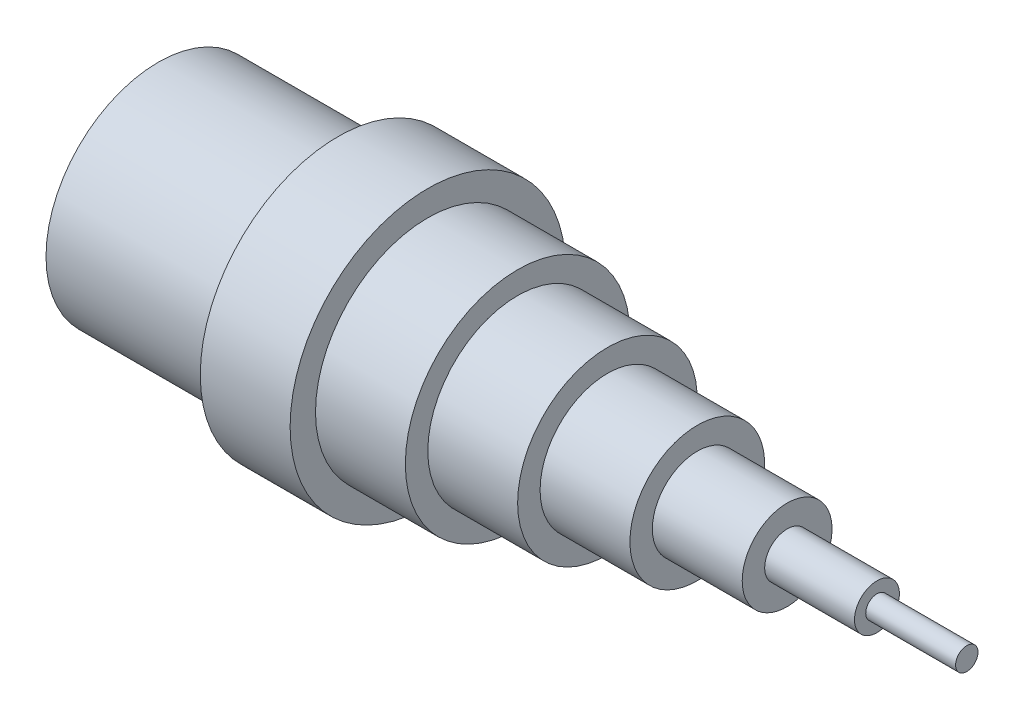
SolidWorks part; units mm, degrees
ref_plane "Front Plane" through (0, 0, 0) normal (0, 0, 1) x (1, 0, 0)
ref_plane "Top Plane" through (0, 0, 0) normal (0, 1, 0) x (1, 0, 0)
ref_plane "Right Plane" through (0, 0, 0) normal (1, 0, 0) x (0, 0, -1)
sketch "Sketch1" plane through (0, 0, 0) normal (0, 0, 1) x (1, 0, 0)
  line L0 (0, 0) -> (195.8104, 0) construction
  line L1 (0, 0) -> (0, 25)
  line L2 (0, 25) -> (40, 25)
  line L3 (40, 25) -> (40, 30.6539)
  line L4 (40, 30.6539) -> (60, 30.6539)
  line L5 (60, 30.6539) -> (60, 25)
  line L6 (60, 25) -> (80, 25)
  line L7 (80, 25) -> (80, 20)
  line L8 (80, 20) -> (100, 20)
  line L9 (100, 20) -> (100, 15)
  line L10 (100, 15) -> (120, 15)
  line L11 (120, 15) -> (120, 10)
  line L12 (120, 10) -> (140, 10)
  line L13 (140, 10) -> (140, 5)
  line L14 (140, 5) -> (160, 5)
  line L15 (160, 5) -> (160, 2.5)
  line L16 (160, 2.5) -> (180, 2.5)
  line L17 (180, 2.5) -> (180, 0)
  line L18 (0, 0) -> (180, 0)
  dimension "D1" = 40
  dimension "D2" = 20
  dimension "D3" = 20
  dimension "D4" = 20
  dimension "D5" = 20
  dimension "D6" = 20
  dimension "D7" = 20
  dimension "D8" = 20
  dimension "D9" = 50
  dimension "D10" = 61.3078
  dimension "D11" = 40
  dimension "D12" = 30
  dimension "D13" = 20
  dimension "D14" = 10
  dimension "D15" = 5
revolve "Revolve1" add sketch "Sketch1" angle 360 about L0
sketch "Sketch2" plane through (0, 0, 0) normal (-1, 0, 0) x (0, 0, 1)
  circle A0 centre (0, 0) radius 20
  dimension "D1" = 40
extrude "Cut-Extrude1" cut sketch "Sketch2" against normal blind 40
